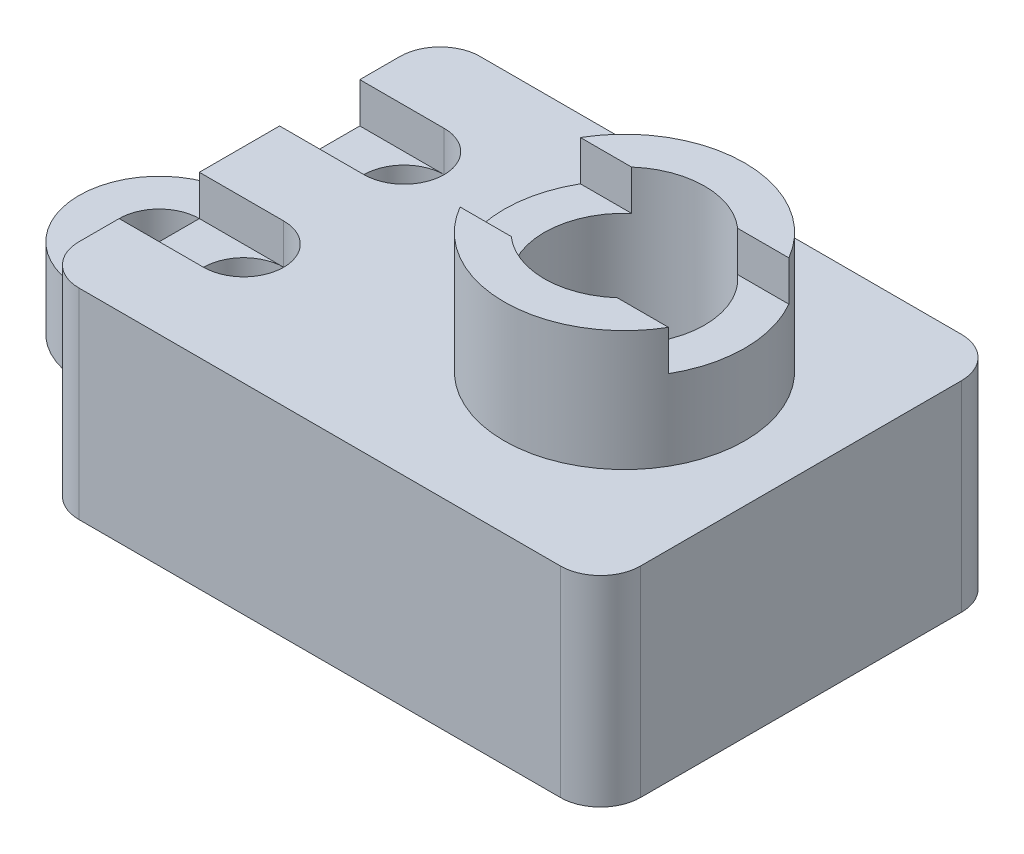
SolidWorks part; units mm, degrees
ref_plane "Front" through (0, 0, 0) normal (0, 0, 1) x (1, 0, 0)
ref_plane "Top" through (0, 0, 0) normal (0, 1, 0) x (1, 0, 0)
ref_plane "Right" through (0, 0, 0) normal (1, 0, 0) x (0, 0, -1)
sketch "Sketch1" plane through (0, 0, 0) normal (0, 1, 0) x (1, 0, 0)
  line L0 (0, 2) -> (1, 2)
  line L1 (0, -2) -> (1, -2)
  line L2 (2, 2.9329) -> (2, 4)
  line L3 (3, -5) -> (15, -5)
  line L4 (2, -4) -> (2, -2.935)
  line L5 (3, 5) -> (15, 5)
  line L6 (16, -4) -> (16, 4)
  circle A0 centre (0, 0) radius 1
  arc A1 (0, 2) -> (0, -2) centre (0, 0) ccw
  arc A2 (1, 2) -> (2.0023, 3) centre (1.0023, 3) ccw
  arc A3 (1, -2) -> (2.0023, -3.0023) centre (1, -3.0023) cw
  arc A4 (2, 4) -> (3, 5) centre (3, 4) cw
  arc A5 (15, 5) -> (16, 4) centre (15, 4) cw
  arc A6 (15, -5) -> (16, -4) centre (15, -4) ccw
  arc A7 (3, -5) -> (2, -4) centre (3, -4) cw
  point P17 (2, 5)
  point P20 (16, 5)
  point P23 (16, -5)
  dimension "D1" = 2
  dimension "D2" = 4
  dimension "D5" = 1.0023
  dimension "D8" = 1
  dimension "D13" = 1
  dimension "D3" = 1
  dimension "D4" = 1
  dimension "D6" = 1
  dimension "D7" = 1.0023
  dimension "D9" = 10
  dimension "D10" = 5
  dimension "D11" = 14
  dimension "D12" = 2
extrude "Boss-Extrude1" add sketch "Sketch1" along normal blind 5
sketch "Sketch3" plane through (0, 0, 0) normal (0, -1, 0) x (1, 0, 0)
  line L0 (16, 4) -> (16, -4) construction
  line L1 (3, -4) -> (15, -4)
  line L2 (3, -4) -> (3, 4)
  line L3 (3, 4) -> (15, 4)
  line L4 (15, -4) -> (15, 4)
  line L5 (3, 5) -> (15, 5) construction
  line L6 (3, -5) -> (15, -5) construction
  line L7 (2, -2.9329) -> (2, -4) construction
  dimension "D1" = 1
  dimension "D2" = 1
  dimension "D3" = 1
  dimension "D4" = 1
extrude "Cut-Extrude1" cut sketch "Sketch3" against normal blind 3
sketch "Sketch4" plane through (0, 5, 0) normal (0, 1, 0) x (1, 0, 0)
  circle A0 centre (11.5979, 0) radius 3
  circle A1 centre (11.5979, 0) radius 2
  dimension "D1" = 4
  dimension "D2" = 6
extrude "Boss-Extrude2" add sketch "Sketch4" along normal blind 3
sketch "Sketch5" plane through (2, 0, 0) normal (-1, 0, 0) x (0, 0, 1)
  line L0 (2, 8) -> (-2, 8) construction
  line L1 (1.5, 8) -> (-1.5, 8)
  line L2 (1.5, 8) -> (1.5, 7)
  line L3 (1.5, 7) -> (-1.5, 7)
  line L4 (-1.5, 8) -> (-1.5, 7)
  line L5 (2, 5) -> (2, 8) construction
  line L6 (-2, 8) -> (-2, 5) construction
  dimension "D1" = 1
  dimension "D2" = 0.5
  dimension "D3" = 0.5
extrude "Cut-Extrude2" cut sketch "Sketch5" against normal blind 17
sketch "Sketch6" plane through (0, 8, 0) normal (0, 1, 0) x (1, 0, 0)
  line L0 (3, -5) -> (15, -5) construction
  line L3 (2, 2.9329) -> (-5.0642, 2.9329)
  line L4 (2, 2.9329) -> (2, -5.7845)
  line L5 (2, -5.7845) -> (-5.0642, -5.7845)
  line L6 (-5.0642, 2.9329) -> (-5.0642, -5.7845)
  circle A0 centre (11.5979, 0) radius 2
  circle A1 centre (4.1029, -2) radius 1
  circle A2 centre (4.1029, 2) radius 1
  dimension "D1" = 2
  dimension "D2" = 2
  dimension "D3" = 4
  dimension "D4" = 3
extrude "Cut-Extrude3" cut sketch "Sketch6" against normal blind 6
sketch "Sketch7" plane through (0, 5, 0) normal (0, 1, 0) x (1, 0, 0)
  line L0 (4.1029, -2) -> (0.2526, -2) construction
  line L1 (1, -2) -> (0, -2) construction
  line L2 (4.1029, -3) -> (0.2526, -3)
  line L3 (4.1029, -1) -> (0.2526, -1)
  line L4 (4.1029, 2) -> (0.9442, 2) construction
  line L5 (4.1029, 1) -> (0.9442, 1)
  line L6 (4.1029, 3) -> (0.9442, 3)
  arc A0 (4.1029, -3) -> (4.1029, -1) centre (4.1029, -2) ccw
  arc A1 (0.2526, -1) -> (0.2526, -3) centre (0.2526, -2) ccw
  arc A2 (4.1029, 1) -> (4.1029, 3) centre (4.1029, 2) ccw
  arc A3 (0.9442, 3) -> (0.9442, 1) centre (0.9442, 2) ccw
  point P5 (2.1778, -2)
  point P10 (2.5236, 2)
  dimension "D1" = 1
  dimension "D2" = 1
extrude "Cut-Extrude4" cut sketch "Sketch7" against normal blind 1
